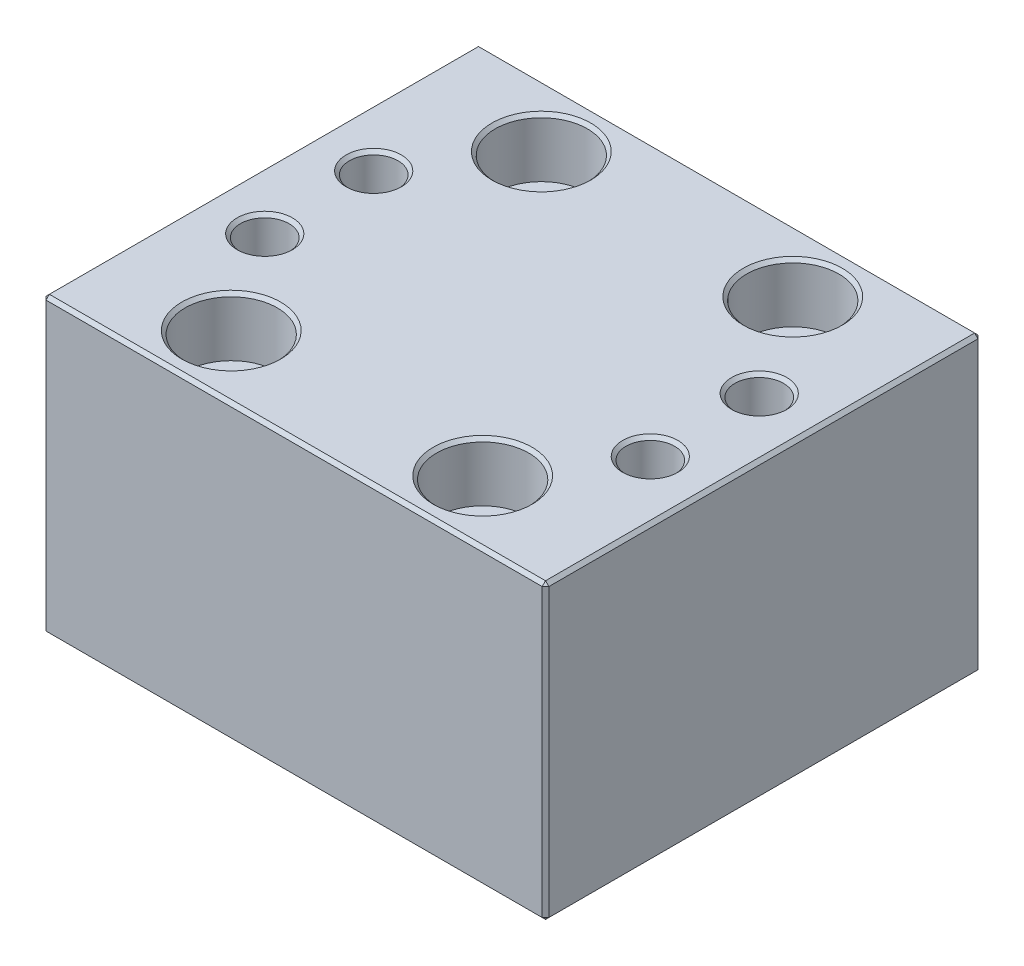
SolidWorks part; units mm, degrees
ref_plane "Front Plane" through (0, 0, 0) normal (0, 0, 1) x (1, 0, 0)
ref_plane "Top Plane" through (0, 0, 0) normal (0, 1, 0) x (1, 0, 0)
ref_plane "Right Plane" through (0, 0, 0) normal (1, 0, 0) x (0, 0, -1)
sketch "Sketch1" plane through (0, 0, 0) normal (0, 1, 0) x (1, 0, 0)
  line L1 (30, -26) -> (-30, -26)
  line L2 (30, -26) -> (30, 26)
  line L3 (30, 26) -> (-30, 26)
  line L4 (-30, -26) -> (-30, 26)
  line L5 (30, -26) -> (-30, 26) construction
  line L6 (30, 26) -> (-30, -26) construction
  line L7 (23, -6.5) -> (-23, -6.5) construction
  line L8 (23, -6.5) -> (23, 6.5) construction
  line L9 (23, 6.5) -> (-23, 6.5) construction
  line L10 (-23, -6.5) -> (-23, 6.5) construction
  line L11 (23, -6.5) -> (-23, 6.5) construction
  line L12 (23, 6.5) -> (-23, -6.5) construction
  line L13 (15, -18.5) -> (-15, -18.5) construction
  line L14 (15, -18.5) -> (15, 18.5) construction
  line L15 (15, 18.5) -> (-15, 18.5) construction
  line L16 (-15, -18.5) -> (-15, 18.5) construction
  line L17 (15, -18.5) -> (-15, 18.5) construction
  line L18 (15, 18.5) -> (-15, -18.5) construction
  circle A0 centre (-23, 6.5) radius 2.9
  circle A1 centre (23, 6.5) radius 2.9
  circle A2 centre (23, -6.5) radius 2.9
  circle A3 centre (-23, -6.5) radius 2.9
  circle A4 centre (-15, 18.5) radius 3.05
  circle A5 centre (15, 18.5) radius 3.05
  circle A6 centre (15, -18.5) radius 3.05
  circle A7 centre (-15, -18.5) radius 3.05
  point P0 (0, 0)
  point P6 (0, 0)
  point P15 (0, 0)
  dimension "D5" = 5.8
  dimension "D6" = 6.1
  dimension "D1" = 52
  dimension "D2" = 60
  dimension "D3" = 13
  dimension "D4" = 46
  dimension "D7" = 30
  dimension "D8" = 37
extrude "Boss-Extrude1" add sketch "Sketch1" along normal blind 35
sketch "Sketch2" plane through (0, 35, 0) normal (0, 1, 0) x (1, 0, 0)
  circle A0 centre (-15, 18.5) radius 5.5
  circle A1 centre (15, 18.5) radius 5.5
  circle A2 centre (15, -18.5) radius 5.5
  circle A3 centre (-15, -18.5) radius 5.5
  dimension "D1" = 11
extrude "Cut-Extrude1" cut sketch "Sketch2" against normal blind 7
chamfer "Chamfer1" distance 0.4 angle 45 20 edges at (-23, 35, 9.4) (23, 35, -3.6) (0, 0, -26) (-30, 17.5, -26) (-30, 0, 0) (30, 17.5, -26) (30, 0, 0) (-30, 17.5, 26) (0, 0, 26) (30, 17.5, 26) (0, 35, -26) (30, 35, 0) (0, 35, 26) (-30, 35, 0) (-23, 35, -3.6) (23, 35, 9.4) (-15, 35, -13) (15, 35, -13) (15, 35, 24) (-15, 35, 24)
